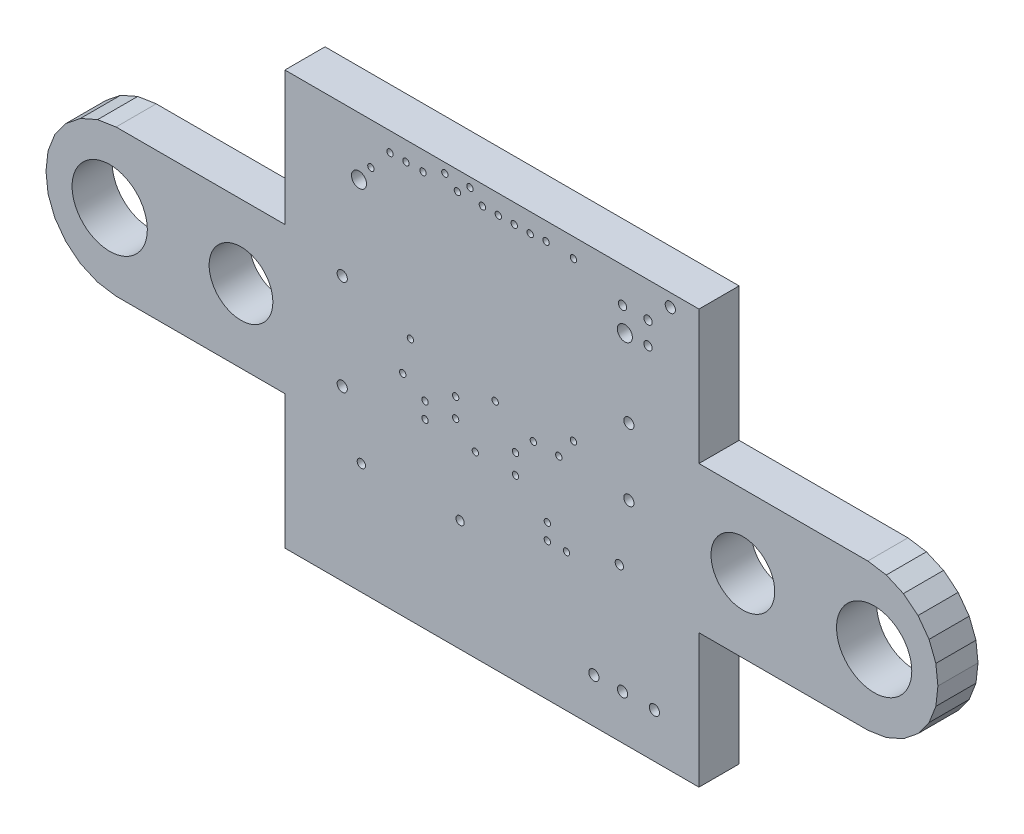
SolidWorks part; units mm, degrees
ref_plane "Спереди" through (0, 0, 0) normal (0, 0, 1) x (1, 0, 0)
ref_plane "Сверху" through (0, 0, 0) normal (0, 1, 0) x (1, 0, 0)
ref_plane "Справа" through (0, 0, 0) normal (1, 0, 0) x (0, 0, -1)
ref_plane "Dielectric_Layer Layer 1" through (0, 0, 1.6) normal (0, 0, 1) x (1, 0, 0)
sketch "Sketch1" plane through (0, 0, 0) normal (0, 0, 1) x (1, 0, 0)
  line L0 (0, 16.51) -> (0, 11.176)
  line L1 (0, 11.176) -> (-6.731, 11.176)
  line L2 (-6.731, 11.176) -> (-7.4684, 11.0622)
  line L3 (-7.4684, 11.0622) -> (-8.1512, 10.7614)
  line L4 (-8.1512, 10.7614) -> (-8.733, 10.2942)
  line L5 (-8.733, 10.2942) -> (-9.1739, 9.6923)
  line L6 (-9.1739, 9.6923) -> (-9.4441, 8.9967)
  line L7 (-9.4441, 8.9967) -> (-9.525, 8.255)
  line L8 (-9.525, 8.255) -> (-9.4441, 7.5133)
  line L9 (-9.4441, 7.5133) -> (-9.1739, 6.8177)
  line L10 (-9.1739, 6.8177) -> (-8.733, 6.2158)
  line L11 (-8.733, 6.2158) -> (-8.1512, 5.7486)
  line L12 (-8.1512, 5.7486) -> (-7.4684, 5.4478)
  line L13 (-7.4684, 5.4478) -> (-6.731, 5.334)
  line L14 (-6.731, 5.334) -> (0, 5.334)
  line L15 (0, 5.334) -> (0, 0)
  line L16 (0, 0) -> (16.51, 0)
  line L17 (16.51, 0) -> (16.51, 5.334)
  line L18 (16.51, 5.334) -> (23.241, 5.334)
  line L19 (23.241, 5.334) -> (23.9784, 5.4478)
  line L20 (23.9784, 5.4478) -> (24.6612, 5.7486)
  line L21 (24.6612, 5.7486) -> (25.243, 6.2158)
  line L22 (25.243, 6.2158) -> (25.6839, 6.8177)
  line L23 (25.6839, 6.8177) -> (25.9541, 7.5133)
  line L24 (25.9541, 7.5133) -> (26.035, 8.255)
  line L25 (26.035, 8.255) -> (25.9541, 8.9967)
  line L26 (25.9541, 8.9967) -> (25.6839, 9.6923)
  line L27 (25.6839, 9.6923) -> (25.243, 10.2942)
  line L28 (25.243, 10.2942) -> (24.6612, 10.7614)
  line L29 (24.6612, 10.7614) -> (23.9784, 11.0622)
  line L30 (23.9784, 11.0622) -> (23.241, 11.176)
  line L31 (23.241, 11.176) -> (16.51, 11.176)
  line L32 (16.51, 11.176) -> (16.51, 16.51)
  line L33 (16.51, 16.51) -> (0, 16.51)
extrude "Board_Outline" add sketch "Sketch1" along normal blind 1.6 separate body
sketch "Sketch2" plane through (0, 0, 0) normal (0, 0, 1) x (1, 0, 0)
  circle A0 centre (13.555, 14.2) radius 0.3
  circle A1 centre (2.955, 14.2) radius 0.3
  circle A2 centre (9.1948, 7.8994) radius 0.127
  circle A3 centre (10.4648, 5.4864) radius 0.127
  circle A4 centre (11.2268, 5.4864) radius 0.127
  circle A5 centre (10.4648, 6.1214) radius 0.127
  circle A6 centre (10.414, 15.7988) radius 0.127
  circle A7 centre (5.005, 9.727) radius 0.127
  circle A8 centre (6.8072, 8.636) radius 0.127
  circle A9 centre (4.699, 8.382) radius 0.127
  circle A10 centre (10.922, 8.636) radius 0.127
  circle A11 centre (6.378, 16.129) radius 0.127
  circle A12 centre (6.8072, 7.874) radius 0.127
  circle A13 centre (6.878, 15.748) radius 0.127
  circle A14 centre (7.378, 16.141) radius 0.127
  circle A15 centre (7.5946, 7.1186) radius 0.127
  circle A16 centre (8.509, 15.748) radius 0.127
  circle A17 centre (5.588, 7.239) radius 0.127
  circle A18 centre (9.779, 15.748) radius 0.127
  circle A19 centre (9.906, 8.636) radius 0.127
  circle A20 centre (9.194, 7.112) radius 0.127
  circle A21 centre (9.144, 15.748) radius 0.127
  circle A22 centre (5.588, 7.874) radius 0.127
  circle A23 centre (13.335, 6.096) radius 0.1651
  circle A24 centre (12.319, 1.778) radius 0.2032
  circle A25 centre (13.716, 8.509) radius 0.2032
  circle A26 centre (2.286, 6.731) radius 0.2032
  circle A27 centre (6.985, 4.445) radius 0.1651
  circle A28 centre (3.048, 4.445) radius 0.1651
  circle A29 centre (11.505, 9.45) radius 0.127
  circle A30 centre (8.386, 9.267) radius 0.127
  circle A31 centre (4.826, 15.748) radius 0.127
  circle A32 centre (4.191, 15.748) radius 0.127
  circle A33 centre (-6.985, 8.255) radius 1.5
  circle A34 centre (23.495, 8.255) radius 1.5
  circle A35 centre (13.716, 11.176) radius 0.2032
  circle A36 centre (2.286, 10.541) radius 0.2032
  circle A37 centre (14.478, 15.113) radius 0.1651
  circle A38 centre (13.462, 15.113) radius 0.1651
  circle A39 centre (14.478, 14.224) radius 0.1651
  circle A40 centre (5.505, 15.748) radius 0.127
  circle A41 centre (3.429, 14.859) radius 0.127
  circle A42 centre (7.874, 15.748) radius 0.127
  circle A43 centre (11.5062, 15.748) radius 0.127
  circle A44 centre (13.462, 1.778) radius 0.2032
  circle A45 centre (14.732, 1.778) radius 0.2032
  circle A46 centre (15.367, 16.002) radius 0.2032
extrude "NPTH" cut sketch "Sketch2" along normal through all
sketch "Sketch3" plane through (0, 0, 0) normal (0, 0, 1) x (1, 0, 0)
  circle A0 centre (-1.75, 8.26) radius 1.27
  circle A1 centre (18.26, 8.26) radius 1.27
extrude "PTH" cut sketch "Sketch3" along normal through all
